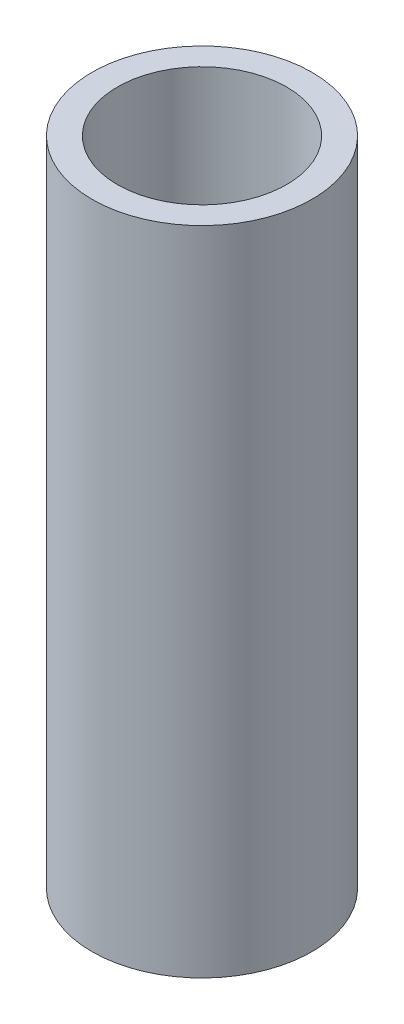
SolidWorks part; units mm, degrees
ref_plane "Front Plane" through (0, 0, 0) normal (0, 0, 1) x (1, 0, 0)
ref_plane "Top Plane" through (0, 0, 0) normal (0, 1, 0) x (1, 0, 0)
ref_plane "Right Plane" through (0, 0, 0) normal (1, 0, 0) x (0, 0, -1)
sketch "Sketch1" plane through (0, 0, 0) normal (0, 1, 0) x (1, 0, 0)
  circle A0 centre (0, 0) radius 1.3
  dimension "D1" = 2.6
extrude "Boss-Extrude1" add sketch "Sketch1" along normal blind 7.7
sketch "Sketch2" plane through (0, 7.7, 0) normal (0, 1, 0) x (1, 0, 0)
  circle A0 centre (0, 0) radius 1
  dimension "D1" = 2
extrude "Cut-Extrude1" cut sketch "Sketch2" against normal blind 7.2
sketch "Sketch3" plane through (0, 0, 0) normal (0, -1, 0) x (1, 0, 0)
  circle A0 centre (0, 0) radius 0.5
  dimension "D1" = 1
extrude "Cut-Extrude2" cut sketch "Sketch3" against normal up to next
